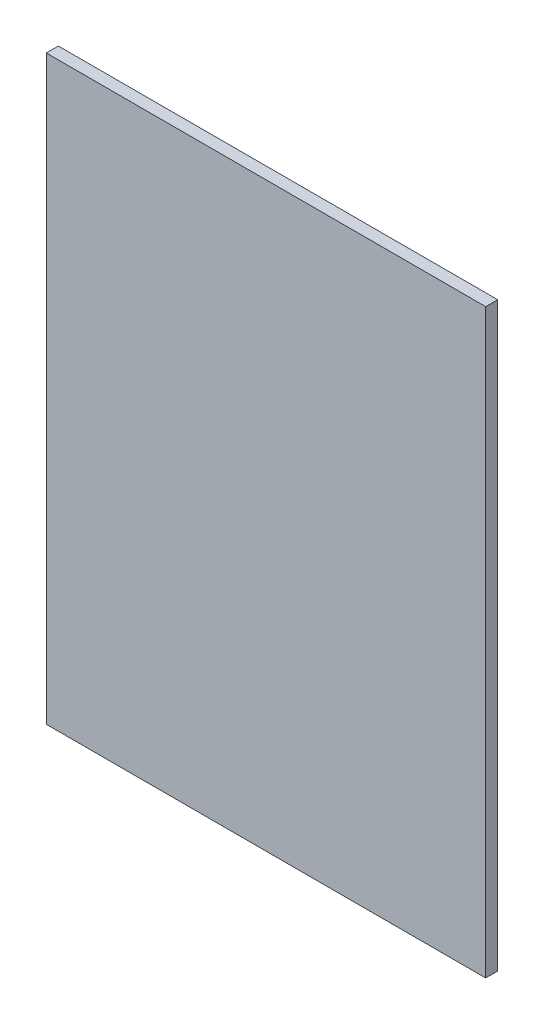
SolidWorks part; units mm, degrees
ref_plane "Front Plane" through (0, 0, 0) normal (0, 0, 1) x (1, 0, 0)
ref_plane "Top Plane" through (0, 0, 0) normal (0, 1, 0) x (1, 0, 0)
ref_plane "Right Plane" through (0, 0, 0) normal (1, 0, 0) x (0, 0, -1)
sketch "Sketch1" plane through (0, 0, 0) normal (0, 0, 1) x (1, 0, 0)
  line L1 (0, 0) -> (109.6, 0)
  line L2 (0, 0) -> (0, -145)
  line L3 (0, -145) -> (109.6, -145)
  line L4 (109.6, 0) -> (109.6, -145)
  dimension "D1" = 145
  dimension "D2" = 109.6
extrude "Boss-Extrude1" add sketch "Sketch1" along normal blind 3
